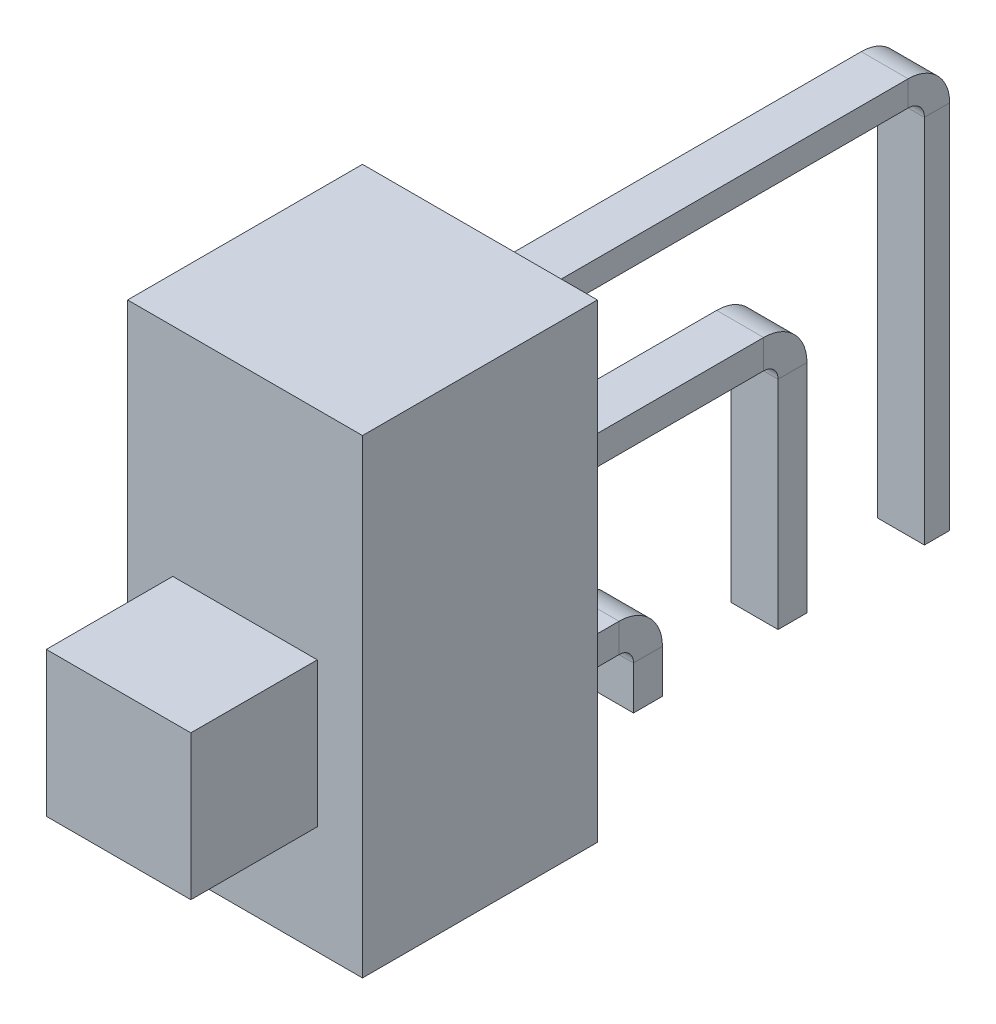
SolidWorks part; units mm, degrees
ref_plane "Přední rovina" through (0, 0, 0) normal (0, 0, 1) x (1, 0, 0)
ref_plane "Horní rovina" through (0, 0, 0) normal (0, 1, 0) x (1, 0, 0)
ref_plane "Pravá rovina" through (0, 0, 0) normal (1, 0, 0) x (0, 0, -1)
sketch "Skica1" plane through (0, 0, 0) normal (0, 1, 0) x (1, 0, 0)
  line L1 (-3.25, 3.25) -> (3.25, 3.25)
  line L2 (-3.25, 3.25) -> (-3.25, -3.25)
  line L3 (-3.25, -3.25) -> (3.25, -3.25)
  line L4 (3.25, 3.25) -> (3.25, -3.25)
  line L5 (-3.25, 3.25) -> (3.25, -3.25) construction
  line L6 (-3.25, -3.25) -> (3.25, 3.25) construction
  point P0 (0, 0)
  dimension "D1" = 6.5
  dimension "D2" = 6.5
extrude "Přidat vysunutím1" add sketch "Skica1" along normal blind 13
sketch "Skica2" plane through (0, 0, 3.25) normal (0, 0, 1) x (1, 0, 0)
  line L0 (-3.25, 13) -> (3.25, 13) construction
  line L1 (-2, 7) -> (2, 7)
  line L2 (-2, 7) -> (-2, 3)
  line L3 (-2, 3) -> (2, 3)
  line L4 (2, 7) -> (2, 3)
  line L5 (-2, 7) -> (2, 3) construction
  line L6 (-2, 3) -> (2, 7) construction
  line L7 (0, -0.8003) -> (0, 13.5932) construction
  point P0 (0, 5)
  point P10 (0, 0)
  dimension "D1" = 6
  dimension "D2" = 4
  dimension "D3" = 4
extrude "Přidat vysunutím2" add sketch "Skica2" along normal blind 3.5
sketch "Skica3" plane through (0, 0, -3.25) normal (0, 0, -1) x (-1, 0, 0)
  line L0 (0, 13.5348) -> (0, -0.8348) construction
  line L1 (-3.25, 13) -> (3.25, 13) construction
  line L2 (-0.65, 11.4) -> (0.65, 11.4)
  line L3 (-0.65, 11.4) -> (-0.65, 10.7)
  line L4 (-0.65, 10.7) -> (0.65, 10.7)
  line L5 (0.65, 11.4) -> (0.65, 10.7)
  line L6 (-0.65, 11.4) -> (0.65, 10.7) construction
  line L7 (-0.65, 10.7) -> (0.65, 11.4) construction
  point P3 (0, 11.05)
  dimension "D1" = 1.3
  dimension "D2" = 0.7
  dimension "D5" = 1.6
sketch "Skica4" plane through (0, 0, 0) normal (1, 0, 0) x (0, 0, -1)
  line L0 (3.25, 11.05) -> (14.45, 11.05)
  line L1 (15.25, 10.25) -> (15.25, 0)
  line L6 (0, 0) -> (16.4537, 0) construction
  arc A2 (14.45, 11.05) -> (15.25, 10.25) centre (14.45, 10.25) cw
  point P3 (16.4537, 0)
  point P15 (0, 0)
  point P16 (0, 0)
  point P17 (0, 0)
  point P24 (15.25, 11.05)
  dimension "D1" = 12
sweep "Táhnout po křivce1" add profiles "Skica3" path "Skica4"
sketch "Skica5" plane through (0, 0, -3.25) normal (0, 0, -1) x (-1, 0, 0)
  line L0 (0, 0) -> (0, 14.378) construction
  line L1 (-0.65, 7.2) -> (0.65, 7.2)
  line L2 (-0.65, 7.2) -> (-0.65, 6.4)
  line L3 (-0.65, 6.4) -> (0.65, 6.4)
  line L4 (0.65, 7.2) -> (0.65, 6.4)
  line L5 (-0.65, 7.2) -> (0.65, 6.4) construction
  line L6 (-0.65, 6.4) -> (0.65, 7.2) construction
  line L7 (-3.25, 0) -> (3.25, 0) construction
  line L8 (-0.65, 10.7) -> (0.65, 10.7) construction
  point P0 (0, 6.8)
  point P9 (0, 0)
  dimension "D1" = 1.3
  dimension "D2" = 0.8
  dimension "D3" = 3.5
sketch "Skica6" plane through (0, 0, 0) normal (1, 0, 0) x (0, 0, -1)
  line L0 (3.25, 6.8) -> (10.45, 6.8)
  line L1 (11.25, 6) -> (11.25, 0)
  line L2 (0, 0) -> (18.825, 0) construction
  arc A0 (10.45, 6.8) -> (11.25, 6) centre (10.45, 6) cw
  dimension "D1" = 0.8
  dimension "D2" = 8
sweep "Táhnout po křivce2" add profiles "Skica5" path "Skica6"
sketch "Skica7" plane through (0, 0, -3.25) normal (0, 0, -1) x (-1, 0, 0)
  line L0 (0, -0.7583) -> (0, 14.3103) construction
  line L1 (-0.65, 2.4) -> (0.65, 2.4)
  line L2 (-0.65, 2.4) -> (-0.65, 1.6)
  line L3 (-0.65, 1.6) -> (0.65, 1.6)
  line L4 (0.65, 2.4) -> (0.65, 1.6)
  line L5 (-0.65, 2.4) -> (0.65, 1.6) construction
  line L6 (-0.65, 1.6) -> (0.65, 2.4) construction
  line L7 (-3.25, 0) -> (3.25, 0) construction
  point P0 (0, 2)
  point P8 (0, 0)
  point P9 (0, 14.3103)
  dimension "D1" = 1.3
  dimension "D2" = 0.8
  dimension "D3" = 1.6
sketch "Skica8" plane through (0, 0, 0) normal (1, 0, 0) x (0, 0, -1)
  line L0 (3.25, 2) -> (6.45, 2)
  line L1 (7.25, 1.2) -> (7.25, 0)
  line L2 (0, 0) -> (20.9049, 0) construction
  arc A0 (6.45, 2) -> (7.25, 1.2) centre (6.45, 1.2) cw
  point P7 (0, 0)
  dimension "D2" = 0.8
  dimension "D1" = 4
sweep "Táhnout po křivce3" add profiles "Skica7" path "Skica8"
